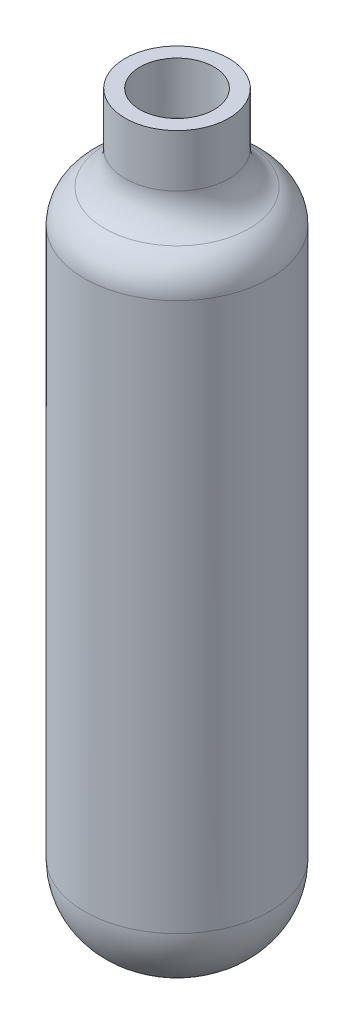
SolidWorks part; units mm, degrees
ref_plane "Ebene vorne" through (0, 0, 0) normal (0, 0, 1) x (1, 0, 0)
ref_plane "Ebene oben" through (0, 0, 0) normal (0, 1, 0) x (1, 0, 0)
ref_plane "Ebene rechts" through (0, 0, 0) normal (1, 0, 0) x (0, 0, -1)
sketch "Skizze1" plane through (0, 0, 0) normal (0, 0, 1) x (1, 0, 0)
  line L0 (0, 0) -> (0, 238.222) construction
  line L1 (0, 0) -> (25, 0)
  line L2 (25, 0) -> (25, 178)
  line L3 (25, 178) -> (14, 178)
  line L4 (14, 178) -> (14, 200)
  line L6 (0, 1) -> (24, 1)
  line L7 (24, 1) -> (24, 177)
  line L8 (24, 177) -> (13, 177)
  line L11 (0, 1) -> (0, 0)
  line L13 (14, 200) -> (10, 200)
  line L14 (13, 177) -> (13, 199) construction
  line L15 (13, 199) -> (0, 199) construction
  line L16 (14, 200) -> (0, 200) construction
  line L17 (13, 177) -> (10, 177)
  line L18 (10, 177) -> (10, 200)
  point P14 (12, 200)
  dimension "D2" = 50
  dimension "D3" = 20
  dimension "D4" = 200
  dimension "D5" = 28
  dimension "D6" = 22
  dimension "D1" = 1
revolve "Rotation1" add sketch "Skizze1" angle 360 about L0
fillet "Verrundung1" radius 20 2 edges at (0, 0, -25) (0, 1, -24)
fillet "Verrundung4" radius 10 2 edges at (0, 178, -25) (0, 177, -24)
fillet "Verrundung5" radius 10 2 edges at (0, 178, -14) (0, 177, -10)
